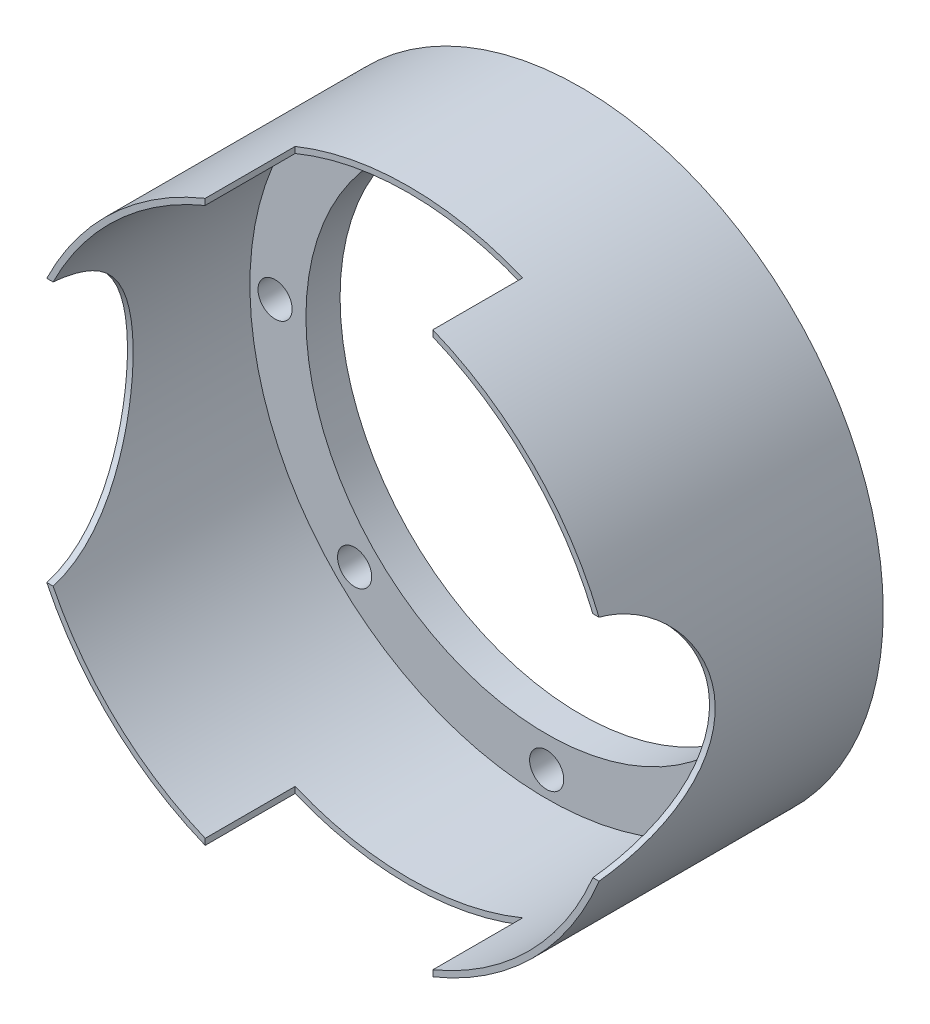
SolidWorks part; units mm, degrees
material "6063-T4"
ref_plane "Front Plane" through (0, 0, 0) normal (0, 0, 1) x (1, 0, 0)
ref_plane "Top Plane" through (0, 0, 0) normal (0, 1, 0) x (1, 0, 0)
ref_plane "Right Plane" through (0, 0, 0) normal (1, 0, 0) x (0, 0, -1)
sketch "Sketch1" plane through (0, 0, 0) normal (0, 0, 1) x (1, 0, 0)
  line L0 (0, 0) -> (490.2841, 0) construction
  line L1 (0, 0) -> (350.0755, 350.0755) construction
  line L2 (0, 0) -> (-298.905, 298.905) construction
  line L3 (0, 0) -> (-282.8341, -282.8341) construction
  line L4 (0, 0) -> (233.7979, -233.7979) construction
  line L5 (0, 0) -> (0, 312.9098) construction
  line L6 (0, 0) -> (-348.2385, 0) construction
  line L7 (0, 0) -> (0, -336.5434) construction
  line L8 (0, 0) -> (425.213, 113.9355) construction
  line L9 (0, 0) -> (-424.8399, 113.8355) construction
  line L10 (0, 0) -> (-167.2069, -403.6731) construction
  circle A0 centre (0, 0) radius 211.5
  circle A1 centre (0, 0) radius 265.7
  circle A2 centre (0, 0) radius 238.6 construction
  circle A3 centre (238.6, 0) radius 20
  circle A4 centre (168.7157, 168.7157) radius 20
  circle A5 centre (0, 238.6) radius 20
  circle A6 centre (-168.7157, 168.7157) radius 20
  circle A7 centre (-238.6, 0) radius 20
  circle A8 centre (-168.7157, -168.7157) radius 20
  circle A9 centre (0, -238.6) radius 20
  circle A10 centre (168.7157, -168.7157) radius 20
  circle A11 centre (230.4699, 61.7542) radius 5
  circle A12 centre (-230.4699, 61.7542) radius 5
  circle A13 centre (-91.3083, -220.4377) radius 5
  point P13 (168.7157, 168.7157)
  point P14 (238.6, 0)
  point P15 (168.7157, -168.7157)
  point P16 (0, -238.6)
  point P17 (-168.7157, -168.7157)
  point P18 (-238.6, 0)
  point P19 (-168.7157, 168.7157)
  point P20 (0, 238.6)
  point P37 (230.4699, 61.7542)
  point P41 (-230.4699, 61.7542)
  point P42 (-91.3083, -220.4377)
extrude "Extrude1" add sketch "Sketch1" along normal blind 5
sketch "Sketch2" plane through (0, 0, 5) normal (0, 0, 1) x (1, 0, 0)
  circle A0 centre (238.6, 0) radius 15
  circle A1 centre (168.7157, 168.7157) radius 15
  circle A2 centre (0, 238.6) radius 15
  circle A3 centre (-168.7157, 168.7157) radius 15
  circle A4 centre (-238.6, 0) radius 15
  circle A5 centre (-168.7157, -168.7157) radius 15
  circle A6 centre (0, -238.6) radius 15
  circle A7 centre (168.7157, -168.7157) radius 15
  circle A8 centre (0, 0) radius 265.7
  circle A9 centre (0, 0) radius 211.5
  point P0 (238.6, 0)
  point P1 (168.7157, 168.7157)
  point P3 (0, 238.6)
  point P5 (-168.7157, 168.7157)
  point P7 (-238.6, 0)
  point P9 (-168.7157, -168.7157)
  point P11 (168.7157, -168.7157)
  point P13 (0, -238.6)
extrude "Extrude2" add sketch "Sketch2" along normal blind 25
sketch "Sketch3" plane through (0, 0, 30) normal (0, 0, 1) x (1, 0, 0)
  circle A0 centre (0, 0) radius 265.7
  circle A1 centre (0, 0) radius 260.7
extrude "Extrude3" add sketch "Sketch3" along normal blind 200
sketch "Sketch4" plane through (0, 0, 0) normal (1, 0, 0) x (0, 0, -1)
  line L2 (0, 0) -> (-508.4098, 0) construction
  circle A0 centre (-250, 0) radius 102.37
  point P0 (-250, 0)
  dimension "D1" = 250
extrude "Extrude4" cut sketch "Sketch4" along normal through all
sketch "Sketch5" plane through (0, 0, 0) normal (1, 0, 0) x (0, 0, -1)
  circle A0 centre (-250, 0) radius 102.37 construction
  circle A1 centre (-250, 0) radius 117.4
  point P0 (0, 0)
extrude "Extrude5" cut sketch "Sketch5" against normal through all
sketch "Sketch6" plane through (0, 0, 0) normal (0, 1, 0) x (1, 0, 0)
  line L0 (0, 0) -> (0, -346.5578) construction
  line L1 (-239.1939, -230) -> (246.0018, -230) construction
  line L2 (0, -230) -> (-383.6241, -230) construction
  line L3 (0, -230) -> (384.9195, -230) construction
  line L4 (-100, -230) -> (-100, 31.5434) construction
  line L5 (-100, -230) -> (-100, -151)
  line L6 (-100, -151) -> (100, -151)
  line L7 (100, -151) -> (100, -230)
  line L8 (100, -230) -> (-100, -230)
  point P1 (0, -230)
  point P8 (-100, -230)
  point P10 (100, -230)
  point P13 (-100, -151)
  dimension "D2" = 100
  dimension "cut1" = 100
  dimension "cut2" = 79
extrude "Extrude6" cut sketch "Sketch6" against normal through all and the other way through all
equation "\"D2@Sketch6\" = \"cut1\""
